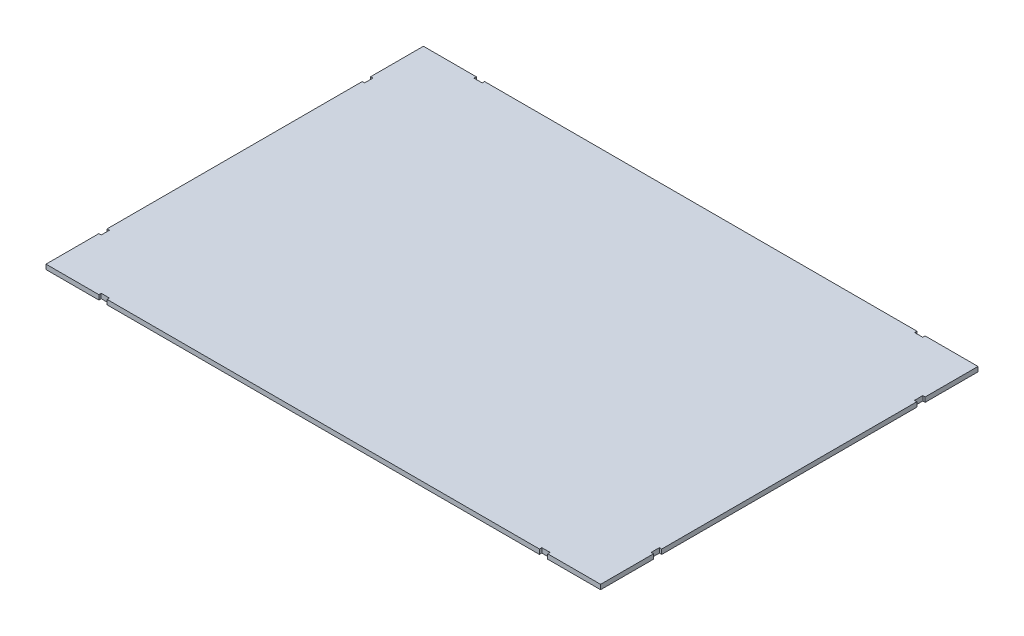
SolidWorks part; units mm, degrees
ref_plane "Front Plane" through (0, 0, 0) normal (0, 0, 1) x (1, 0, 0)
ref_plane "Top Plane" through (0, 0, 0) normal (0, 1, 0) x (1, 0, 0)
ref_plane "Right Plane" through (0, 0, 0) normal (1, 0, 0) x (0, 0, -1)
sketch "Sketch1" plane through (0, 0, 0) normal (0, 1, 0) x (1, 0, 0)
  line L1 (-469.5, -319.5) -> (469.5, -319.5)
  line L2 (-469.5, -319.5) -> (-469.5, 319.5)
  line L3 (-469.5, 319.5) -> (469.5, 319.5)
  line L4 (469.5, -319.5) -> (469.5, 319.5)
  line L5 (-469.5, -319.5) -> (469.5, 319.5) construction
  line L6 (-469.5, 319.5) -> (469.5, -319.5) construction
  point P0 (0, 0)
  dimension "Largura" = 939
  dimension "Profundidade" = 639
extrude "Boss-Extrude1" add sketch "Sketch1" along normal blind 8
sketch "Sketch2" plane through (0, 8, 0) normal (0, 1, 0) x (1, 0, 0)
  line L0 (-469.5, -319.5) -> (469.5, -319.5) construction
  line L1 (-380, -315.5) -> (-366, -315.5)
  line L2 (-380, -315.5) -> (-380, -323.5)
  line L3 (-380, -323.5) -> (-366, -323.5)
  line L4 (-366, -315.5) -> (-366, -323.5)
  line L5 (-380, -315.5) -> (-366, -323.5) construction
  line L6 (-380, -323.5) -> (-366, -315.5) construction
  line L7 (-469.5, 319.5) -> (-469.5, -319.5) construction
  line L8 (0, -319.5) -> (0, 319.5) construction
  line L9 (380, -315.5) -> (366, -315.5)
  line L10 (380, -315.5) -> (380, -323.5)
  line L11 (380, -323.5) -> (366, -323.5)
  line L12 (366, -315.5) -> (366, -323.5)
  line L13 (-469.5, 0) -> (469.5, 0) construction
  line L14 (469.5, -319.5) -> (469.5, 319.5) construction
  line L15 (-380, 315.5) -> (-380, 323.5)
  line L16 (-473.5, -216) -> (-465.5, -216)
  line L17 (-473.5, -216) -> (-473.5, -230)
  line L18 (-473.5, -230) -> (-465.5, -230)
  line L19 (-465.5, -216) -> (-465.5, -230)
  line L20 (-473.5, -216) -> (-465.5, -230) construction
  line L21 (-473.5, -230) -> (-465.5, -216) construction
  line L22 (-380, 323.5) -> (-366, 315.5) construction
  line L23 (-380, 315.5) -> (-366, 323.5) construction
  line L24 (-366, 315.5) -> (-366, 323.5)
  line L25 (-380, 323.5) -> (-366, 323.5)
  line L26 (-380, 315.5) -> (-366, 315.5)
  line L27 (366, 315.5) -> (366, 323.5)
  line L28 (380, 323.5) -> (366, 323.5)
  line L29 (380, 315.5) -> (380, 323.5)
  line L30 (380, 315.5) -> (366, 315.5)
  line L31 (-473.5, 230) -> (-465.5, 216) construction
  line L32 (-473.5, 216) -> (-465.5, 230) construction
  line L33 (-465.5, 216) -> (-465.5, 230)
  line L34 (-473.5, 230) -> (-465.5, 230)
  line L35 (-473.5, 216) -> (-473.5, 230)
  line L36 (-473.5, 216) -> (-465.5, 216)
  line L37 (469.5, 319.5) -> (-469.5, 319.5) construction
  line L38 (473.5, 216) -> (465.5, 230) construction
  line L39 (473.5, 230) -> (465.5, 216) construction
  line L40 (473.5, 216) -> (465.5, 216)
  line L41 (473.5, 216) -> (473.5, 230)
  line L42 (473.5, 230) -> (465.5, 230)
  line L43 (465.5, 216) -> (465.5, 230)
  line L44 (473.5, -230) -> (465.5, -216) construction
  line L45 (473.5, -216) -> (465.5, -230) construction
  line L46 (465.5, -216) -> (465.5, -230)
  line L47 (473.5, -230) -> (465.5, -230)
  line L48 (473.5, -216) -> (473.5, -230)
  line L49 (473.5, -216) -> (465.5, -216)
  point P0 (-373, -319.5)
  point P22 (-469.5, -223)
  point P31 (-373, 319.5)
  point P40 (-469.5, 223)
  point P43 (0, 0)
  point P47 (469.5, 223)
  point P52 (469.5, -223)
  dimension "D1" = 89.5
  dimension "D2" = 14
  dimension "D3" = 4
  dimension "D4" = 89.5
  dimension "D5" = 14
  dimension "D6" = 4
extrude "Cut-Extrude1" cut sketch "Sketch2" against normal through all
